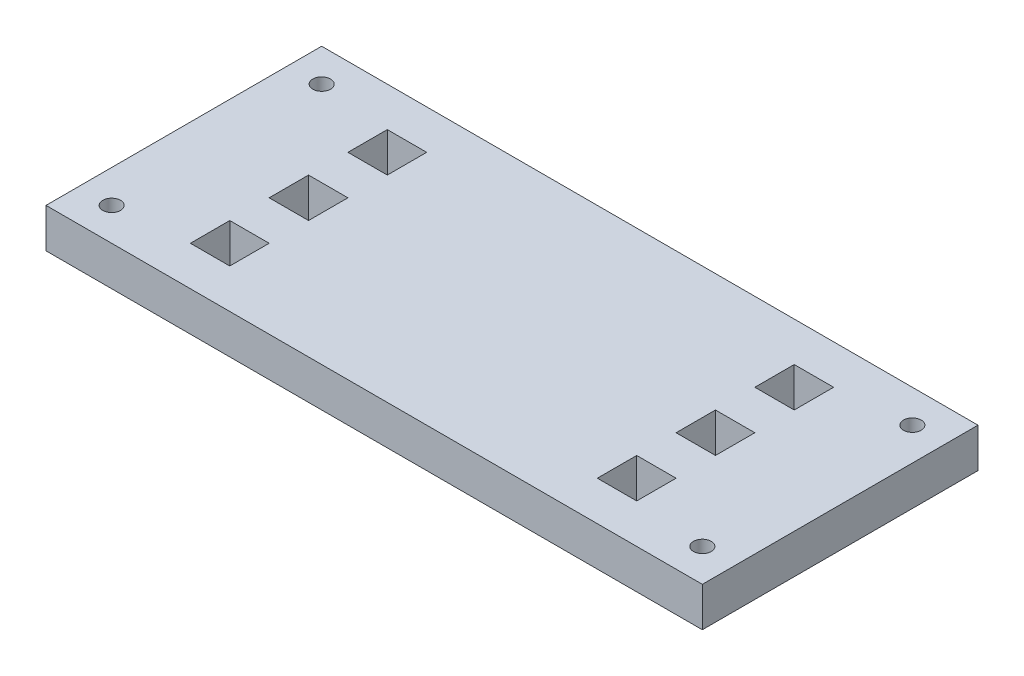
SolidWorks part; units mm, degrees
ref_plane "Front" through (0, 0, 0) normal (0, 0, 1) x (1, 0, 0)
ref_plane "Top" through (0, 0, 0) normal (0, 1, 0) x (1, 0, 0)
ref_plane "Right" through (0, 0, 0) normal (1, 0, 0) x (0, 0, -1)
sketch "Sketch2" plane through (0, 0, 0) normal (0, 1, 0) x (1, 0, 0)
  line L0 (-28, -9) -> (-28, -3) construction
  line L1 (-50, 21) -> (50, 21)
  line L2 (-50, 21) -> (-50, -21)
  line L3 (-50, -21) -> (50, -21)
  line L4 (50, 21) -> (50, -21)
  line L5 (-34, -15) -> (-28, -15)
  line L6 (-34, -15) -> (-34, -9)
  line L7 (-34, -9) -> (-28, -9)
  line L8 (-28, -15) -> (-28, -9)
  line L9 (-34, -3) -> (-28, -3)
  line L10 (-34, -3) -> (-34, 3)
  line L11 (-34, 3) -> (-28, 3)
  line L12 (-28, -3) -> (-28, 3)
  line L13 (-34, 9) -> (-28, 9)
  line L14 (-34, 9) -> (-34, 15)
  line L15 (-34, 15) -> (-28, 15)
  line L16 (-28, 9) -> (-28, 15)
  line L17 (-28, 3) -> (-28, 9) construction
  line L18 (-28, 0) -> (0, 0) construction
  line L19 (50, 0) -> (0, 0) construction
  line L20 (0, 27.9344) -> (0, -28.0812) construction
  line L21 (34, -9) -> (28, -9)
  line L22 (28, -15) -> (28, -9)
  line L23 (34, -15) -> (28, -15)
  line L24 (34, -15) -> (34, -9)
  line L25 (34, 3) -> (28, 3)
  line L26 (28, -3) -> (28, 3)
  line L27 (34, -3) -> (28, -3)
  line L28 (34, -3) -> (34, 3)
  line L29 (34, 15) -> (28, 15)
  line L30 (28, 9) -> (28, 15)
  line L31 (34, 9) -> (28, 9)
  line L32 (34, 9) -> (34, 15)
  line L35 (-45, -16) -> (-50, -16) construction
  line L36 (-45, -16) -> (-45, -21) construction
  circle A3 centre (-45, -16) radius 1.35
  circle A4 centre (-45, 16) radius 1.35
  circle A5 centre (45, 16) radius 1.35
  circle A6 centre (45, -16) radius 1.35
  point P0 (0, 0)
  point P35 (0, 21)
  dimension "D5" = 2.7
  dimension "D1" = 100
  dimension "D2" = 42
  dimension "D3" = 28
  dimension "D4" = 6
  dimension "D6" = 5
  dimension "D7" = 5
extrude "Boss-Extrude1" add sketch "Sketch2" along normal blind 6
